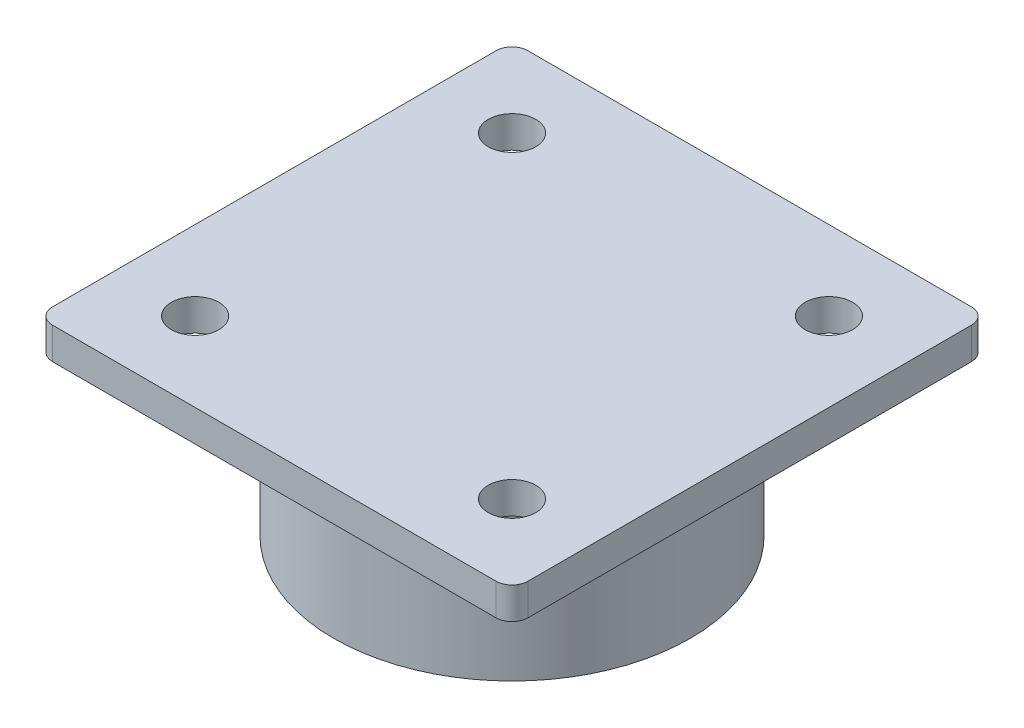
SolidWorks part; units mm, degrees
material "PVC Rigid"
ref_plane "Front Plane" through (0, 0, 0) normal (0, 0, 1) x (1, 0, 0)
ref_plane "Top Plane" through (0, 0, 0) normal (0, 1, 0) x (1, 0, 0)
ref_plane "Right Plane" through (0, 0, 0) normal (1, 0, 0) x (0, 0, -1)
sketch "Sketch2" plane through (0, 0, 0) normal (0, 1, 0) x (1, 0, 0)
  line L0 (38.1, 38.1) -> (-38.1, -38.1) construction
  line L1 (-35.56, 38.1) -> (35.56, 38.1)
  line L2 (-38.1, 35.56) -> (-38.1, -35.56)
  line L3 (-35.56, -38.1) -> (35.56, -38.1)
  line L4 (38.1, 35.56) -> (38.1, -35.56)
  line L5 (-25.4, 25.4) -> (25.4, -25.4) construction
  line L6 (25.4, 25.4) -> (-25.4, 25.4) construction
  line L7 (25.4, 25.4) -> (25.4, -25.4) construction
  line L8 (25.4, -25.4) -> (-25.4, -25.4) construction
  line L9 (-25.4, 25.4) -> (-25.4, -25.4) construction
  circle A0 centre (-25.4, 25.4) radius 3.81
  circle A1 centre (25.4, 25.4) radius 3.81
  circle A2 centre (25.4, -25.4) radius 3.81
  circle A3 centre (-25.4, -25.4) radius 3.81
  arc A4 (35.56, -38.1) -> (38.1, -35.56) centre (35.56, -35.56) ccw
  arc A5 (-38.1, -35.56) -> (-35.56, -38.1) centre (-35.56, -35.56) ccw
  arc A6 (35.56, 38.1) -> (38.1, 35.56) centre (35.56, 35.56) cw
  arc A7 (-35.56, 38.1) -> (-38.1, 35.56) centre (-35.56, 35.56) ccw
  point P23 (-38.1, 38.1)
  dimension "D3" = 7.62
  dimension "D4" = 2.54
  dimension "D1" = 76.2
  dimension "D2" = 50.8
extrude "Boss-Extrude1" add sketch "Sketch2" along normal blind 5.08
sketch "Sketch3" plane through (0, 0, 0) normal (0, -1, 0) x (1, 0, 0)
  circle A0 centre (0, 0) radius 28.575
  dimension "D1" = 57.15
extrude "Boss-Extrude2" add sketch "Sketch3" along normal blind 25.4
sketch "Sketch4" plane through (0, -25.4, 0) normal (0, -1, 0) x (1, 0, 0)
  circle A0 centre (0, 0) radius 24.2824
  dimension "D1" = 48.5648
extrude "Cut-Extrude1" cut sketch "Sketch4" against normal blind 19.05
